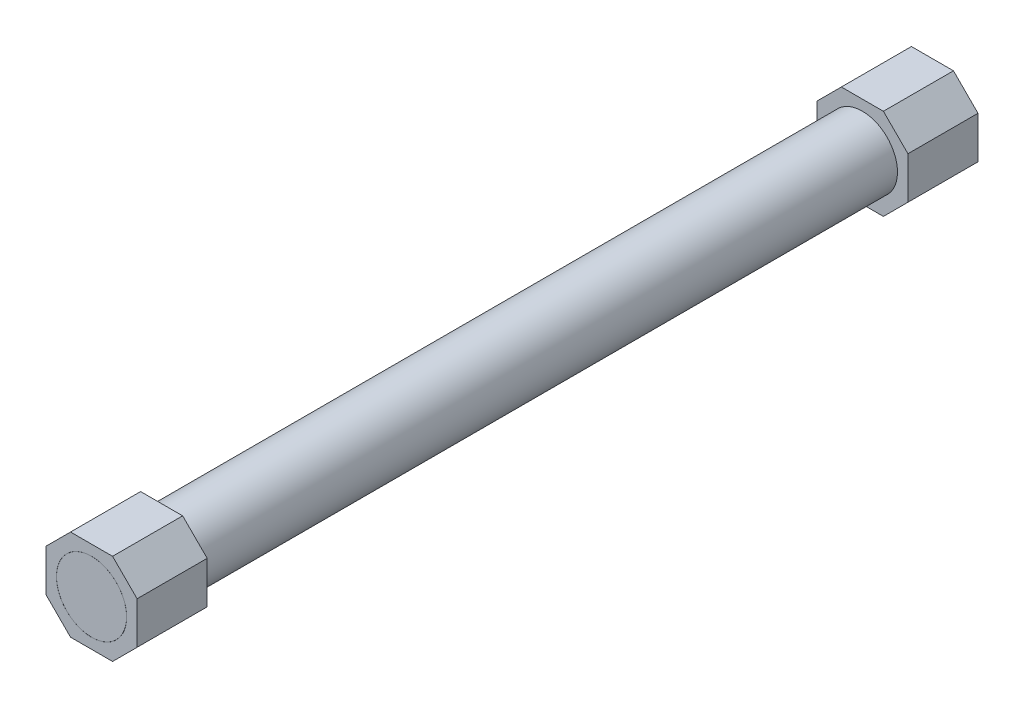
SolidWorks part; units mm, degrees
ref_plane "Front Plane" through (0, 0, 0) normal (0, 0, 1) x (1, 0, 0)
ref_plane "Top Plane" through (0, 0, 0) normal (0, 1, 0) x (1, 0, 0)
ref_plane "Right Plane" through (0, 0, 0) normal (1, 0, 0) x (0, 0, -1)
sketch "Sketch1" plane through (0, 0, 0) normal (0, 0, 1) x (1, 0, 0)
  circle A0 centre (0, 0) radius 5
  dimension "D1" = 10
extrude "Boss-Extrude1" add sketch "Sketch1" along normal blind 120
sketch "Sketch2" plane through (0, 0, 120) normal (0, 0, 1) x (1, 0, 0)
  line L0 (0, 0) -> (0, 6.5) construction
  line L1 (0, 6.5) -> (0, -6.5) construction
  line L2 (3, 6.5) -> (-3, 6.5)
  line L3 (-3, 6.5) -> (-6.5, 3)
  line L4 (-6.5, 3) -> (-6.5, -3)
  line L5 (-6.5, -3) -> (-3, -6.5)
  line L6 (-3, -6.5) -> (3, -6.5)
  line L7 (-6.5, 0) -> (0, 0) construction
  line L8 (6.5, -3) -> (3, -6.5)
  line L9 (6.5, 3) -> (6.5, -3)
  line L10 (3, 6.5) -> (6.5, 3)
  circle A0 centre (0, 0) radius 5.01
  dimension "D6" = 10.02
  dimension "D1" = 6.5
  dimension "D2" = 6.5
  dimension "D3" = 6.5
  dimension "D4" = 3
  dimension "D5" = 6
extrude "Boss-Extrude2" add sketch "Sketch2" against normal blind 10 separate body
ref_plane "Plane1" through (0, 0, 60) normal (0, 0, -1) x (-1, 0, 0)
mirror "Mirror1" about plane through (0, 0, 60) normal (0, 0, -1) of bodies 102
